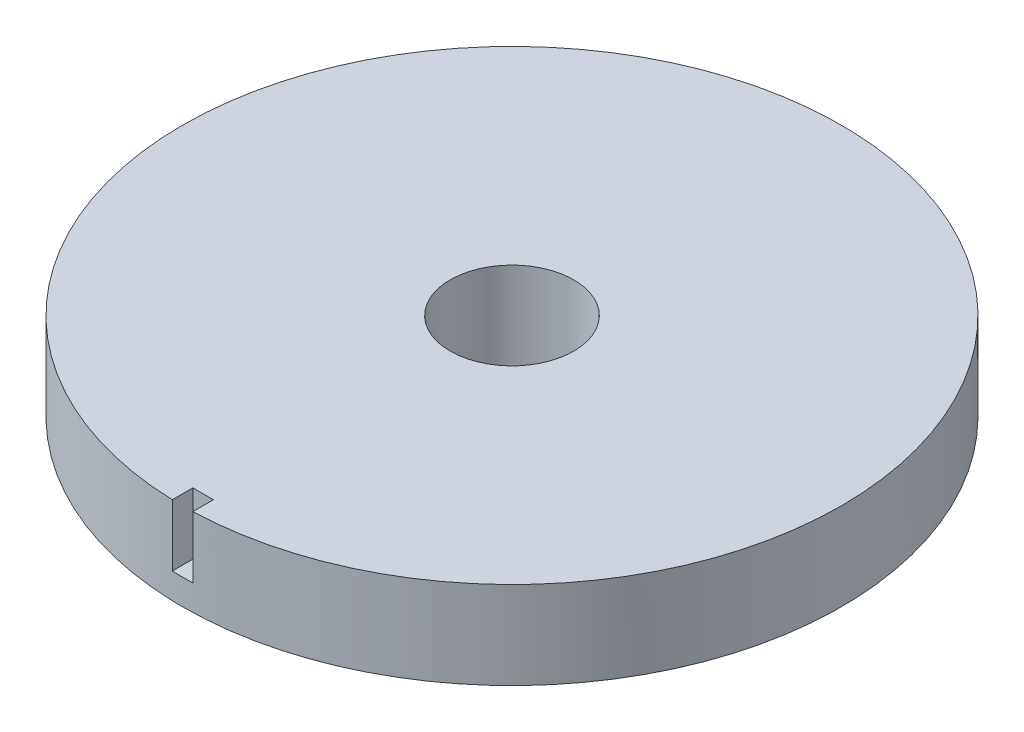
SolidWorks part; units mm, degrees
material "1060 Alloy"
ref_plane "Front Plane" through (0, 0, 0) normal (0, 0, 1) x (1, 0, 0)
ref_plane "Top Plane" through (0, 0, 0) normal (0, 1, 0) x (1, 0, 0)
ref_plane "Right Plane" through (0, 0, 0) normal (1, 0, 0) x (0, 0, -1)
sketch "Sketch1" plane through (0, 0, 0) normal (0, 1, 0) x (1, 0, 0)
  circle A0 centre (0, 0) radius 16
  circle A1 centre (0, 0) radius 3
  dimension "D1" = 32
  dimension "D2" = 6
extrude "Boss-Extrude1" add sketch "Sketch1" along normal blind 4.25
sketch "Sketch2" plane through (0, 0, 0) normal (0, 0, 1) x (1, 0, 0)
  line L0 (0, -55) -> (0, 55) construction
  line L1 (0.5, 1.25) -> (-0.5, 1.25)
  line L2 (0.5, 1.25) -> (0.5, 4.25)
  line L3 (0.5, 4.25) -> (-0.5, 4.25)
  line L4 (-0.5, 1.25) -> (-0.5, 4.25)
  line L5 (0.5, 1.25) -> (-0.5, 4.25) construction
  line L6 (0.5, 4.25) -> (-0.5, 1.25) construction
  line L7 (16, 4.25) -> (-16, 4.25) construction
  point P0 (0, 2.75)
  dimension "D1" = 1
  dimension "D2" = 3
extrude "Cut-Extrude1" cut sketch "Sketch2" against normal blind 1 from surface starting at face at (0, 4.25, 16)
